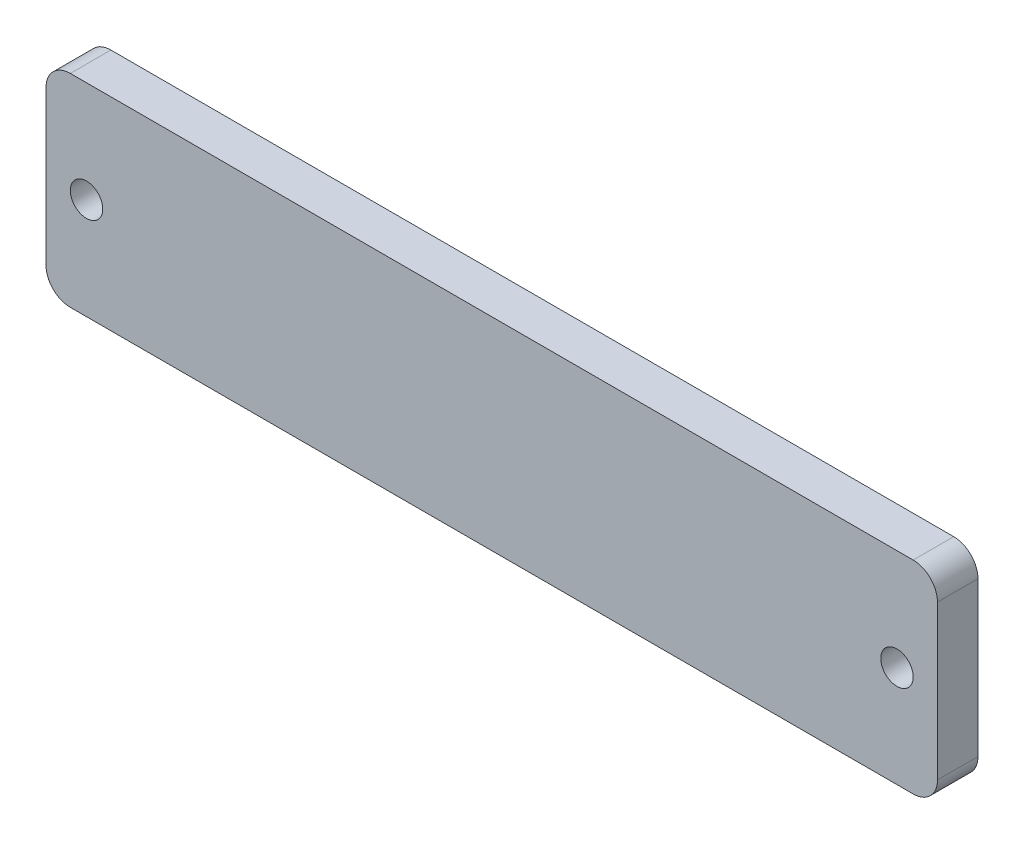
SolidWorks part; units mm, degrees
ref_plane "前视基准面" through (0, 0, 0) normal (0, 0, 1) x (1, 0, 0)
ref_plane "上视基准面" through (0, 0, 0) normal (0, 1, 0) x (1, 0, 0)
ref_plane "右视基准面" through (0, 0, 0) normal (1, 0, 0) x (0, 0, -1)
other "Configuration Table"
sketch "草图1" plane through (0, 0, 0) normal (0, 0, 1) x (1, 0, 0)
  line L1 (-52, 12.5) -> (52, 12.5)
  line L2 (-55, 9.5) -> (-55, -9.5)
  line L3 (-52, -12.5) -> (52, -12.5)
  line L4 (55, 9.5) -> (55, -9.5)
  line L5 (-55, 12.5) -> (55, -12.5) construction
  line L6 (-55, -12.5) -> (55, 12.5) construction
  arc A0 (52, -12.5) -> (55, -9.5) centre (52, -9.5) ccw
  arc A1 (52, 12.5) -> (55, 9.5) centre (52, 9.5) cw
  arc A2 (-55, -9.5) -> (-52, -12.5) centre (-52, -9.5) ccw
  arc A3 (-52, 12.5) -> (-55, 9.5) centre (-52, 9.5) ccw
  point P0 (0, 0)
  dimension "D3" = 3
  dimension "D1" = 110
  dimension "D2" = 25
extrude "凸台-拉伸1" add sketch "草图1" against normal blind 5
sketch "草图2" plane through (0, 0, 0) normal (0, 0, 1) x (1, 0, 0)
  line L0 (-55, 0) -> (55, 0) construction
  line L1 (-55, 9.5) -> (-55, -9.5) construction
  line L2 (55, -9.5) -> (55, 9.5) construction
  line L3 (-50, 12.5) -> (-50, -12.5) construction
  line L4 (52, 12.5) -> (-52, 12.5) construction
  line L5 (-52, -12.5) -> (52, -12.5) construction
  line L6 (50, 12.5) -> (50, -12.5) construction
  circle A0 centre (50, 0) radius 2
  circle A1 centre (-50, 0) radius 2
  point P14 (-45, 0)
  point P15 (45, 0)
  dimension "D3" = 4
  dimension "D4" = 4
  dimension "D1" = 5
  dimension "D2" = 5
extrude "切除-拉伸1" cut sketch "草图2" against normal through all
